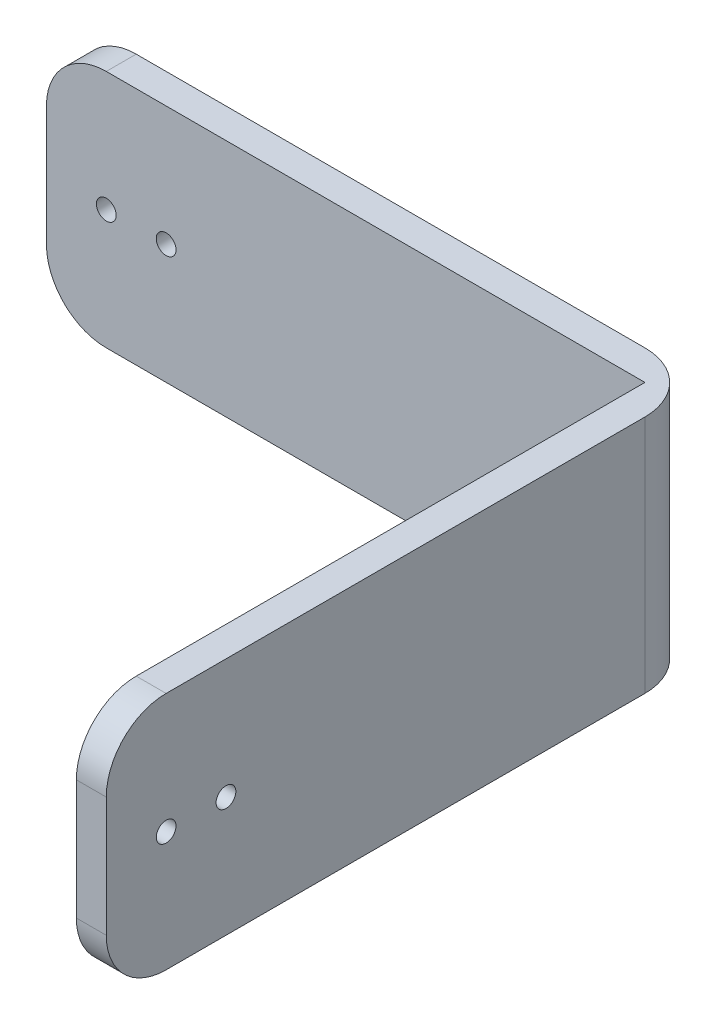
SolidWorks part; units mm, degrees
ref_plane "Plan de face" through (0, 0, 0) normal (0, 0, 1) x (1, 0, 0)
ref_plane "Plan de dessus" through (0, 0, 0) normal (0, 1, 0) x (1, 0, 0)
ref_plane "Plan de droite" through (0, 0, 0) normal (1, 0, 0) x (0, 0, -1)
sketch "Esquisse1" plane through (0, 0, 0) normal (0, 0, 1) x (1, 0, 0)
  line L1 (-52.8295, 27.4148) -> (-34.8295, 27.4148)
  line L2 (-54.8295, 25.4148) -> (-54.8295, 21.4148)
  line L3 (-52.8295, 19.4148) -> (-34.8295, 19.4148)
  line L4 (-34.8295, 27.4148) -> (-34.8295, 19.4148)
  arc A0 (-52.8295, 27.4148) -> (-54.8295, 25.4148) centre (-52.8295, 25.4148) ccw
  arc A1 (-54.8295, 21.4148) -> (-52.8295, 19.4148) centre (-52.8295, 21.4148) ccw
  point P6 (-54.8295, 27.4148)
  dimension "D3" = 2
  dimension "D4" = 2
  dimension "D1" = 20
  dimension "D2" = 8
extrude "Extrusion1" add sketch "Esquisse1" against normal blind 1
sketch "Esquisse4" plane through (-34.8295, 0, 0) normal (1, 0, 0) x (0, 0, -1)
  line L1 (1, 27.4148) -> (-17, 27.4148)
  line L2 (1, 27.4148) -> (1, 19.4148)
  line L3 (1, 19.4148) -> (-17, 19.4148)
  line L4 (-19, 25.4148) -> (-19, 21.4148)
  arc A0 (-19, 25.4148) -> (-17, 27.4148) centre (-17, 25.4148) cw
  arc A1 (-19, 21.4148) -> (-17, 19.4148) centre (-17, 21.4148) ccw
  point P9 (-19, 19.4148)
  dimension "D3" = 2
  dimension "D1" = 20
  dimension "D2" = 8
extrude "Extrusion3" add sketch "Esquisse4" along normal blind 1
hole_wizard "Dégagement #00001" positions "Esquisse3D1" profile "Esquisse5" hole size "#0000" standard "Ansi Pouces" end condition through all
sketch3d "Esquisse3D1"
  line L0 (-34.8295, 27.4148, 0) -> (-52.8295, 27.4148, 0) construction
  line L1 (-54.8295, 25.4148, 0) -> (-54.8295, 21.4148, 0) construction
  point P0 (-52.8295, 23.4148, 0)
  dimension "D1" = 4
  dimension "D2" = 2
sketch "Esquisse5" plane through (-52.8295, 23.4148, 0) normal (1, 0, 0) x (0, -1, 0)
  line L0 (0, 0) -> (0, 1)
  line L1 (0, 1) -> (0.3302, 1)
  line L2 (0.3302, 1) -> (0.3302, 0)
  line L5 (0.3302, 0) -> (0, 0)
  line L11 (0, -6.35) -> (0, 107.95) construction
  dimension "Diamètre du perçage jusqu'au prochain" = 0.6604
  dimension "Profondeur du perçage jusqu'au prochain" = 1
hole_wizard "Dégagement #00002" positions "Esquisse3D2" profile "Esquisse6" hole size "#0000" standard "Ansi Pouces" end condition through all
sketch3d "Esquisse3D2"
  line L0 (-34.8295, 27.4148, 0) -> (-52.8295, 27.4148, 0) construction
  circle A0 centre (-52.8295, 23.4148, 0) radius 0.3302 construction
  point P0 (-50.8295, 23.4148, 0)
  point P5 (-52.8295, 23.4148, 0.3302)
  dimension "D1" = 2
  dimension "D2" = 4
sketch "Esquisse6" plane through (-50.8295, 23.4148, 0) normal (1, 0, 0) x (0, -1, 0)
  line L0 (0, 0) -> (0, 1)
  line L1 (0, 1) -> (0.3302, 1)
  line L2 (0.3302, 1) -> (0.3302, 0)
  line L5 (0.3302, 0) -> (0, 0)
  line L11 (0, -6.35) -> (0, 107.95) construction
  dimension "Diamètre du perçage jusqu'au prochain" = 0.6604
  dimension "Profondeur du perçage jusqu'au prochain" = 1
hole_wizard "Dégagement #00004" positions "Esquisse3D4" profile "Esquisse8" hole size "#0000" standard "Ansi Pouces" end condition through all
sketch3d "Esquisse3D4"
  line L0 (-33.8295, 25.4148, 19) -> (-33.8295, 21.4148, 19) construction
  line L1 (-33.8295, 19.4148, 17) -> (-33.8295, 19.4148, -1) construction
  point P0 (-33.8295, 23.4148, 17)
  dimension "D1" = 2
  dimension "D2" = 4
sketch "Esquisse8" plane through (-33.8295, 23.4148, 17) normal (0, 1, 0) x (0, 0, -1)
  line L0 (0, 0) -> (0, 21)
  line L1 (0, 21) -> (0.3302, 21)
  line L2 (0.3302, 21) -> (0.3302, 0)
  line L5 (0.3302, 0) -> (0, 0)
  line L11 (0, -6.35) -> (0, 107.95) construction
  dimension "Diamètre du perçage jusqu'au prochain" = 0.6604
  dimension "Profondeur du perçage jusqu'au prochain" = 21
hole_wizard "Dégagement #00005" positions "Esquisse3D5" profile "Esquisse9" hole size "#0000" standard "Ansi Pouces" end condition through all
sketch3d "Esquisse3D5"
  line L0 (-33.8295, 19.4148, 17) -> (-33.8295, 19.4148, -1) construction
  circle A0 centre (-33.8295, 23.4148, 17) radius 0.3302 construction
  point P0 (-33.8295, 23.4148, 15)
  point P5 (-33.4993, 23.4148, 17)
  dimension "D1" = 2
  dimension "D2" = 4
sketch "Esquisse9" plane through (-33.8295, 23.4148, 15) normal (0, 1, 0) x (0, 0, -1)
  line L0 (0, 0) -> (0, 21)
  line L1 (0, 21) -> (0.3302, 21)
  line L2 (0.3302, 21) -> (0.3302, 0)
  line L5 (0.3302, 0) -> (0, 0)
  line L11 (0, -6.35) -> (0, 107.95) construction
  dimension "Diamètre du perçage jusqu'au prochain" = 0.6604
  dimension "Profondeur du perçage jusqu'au prochain" = 21
fillet "Congé2" radius 2 1 edges at (-33.8295, 23.4148, -1)
